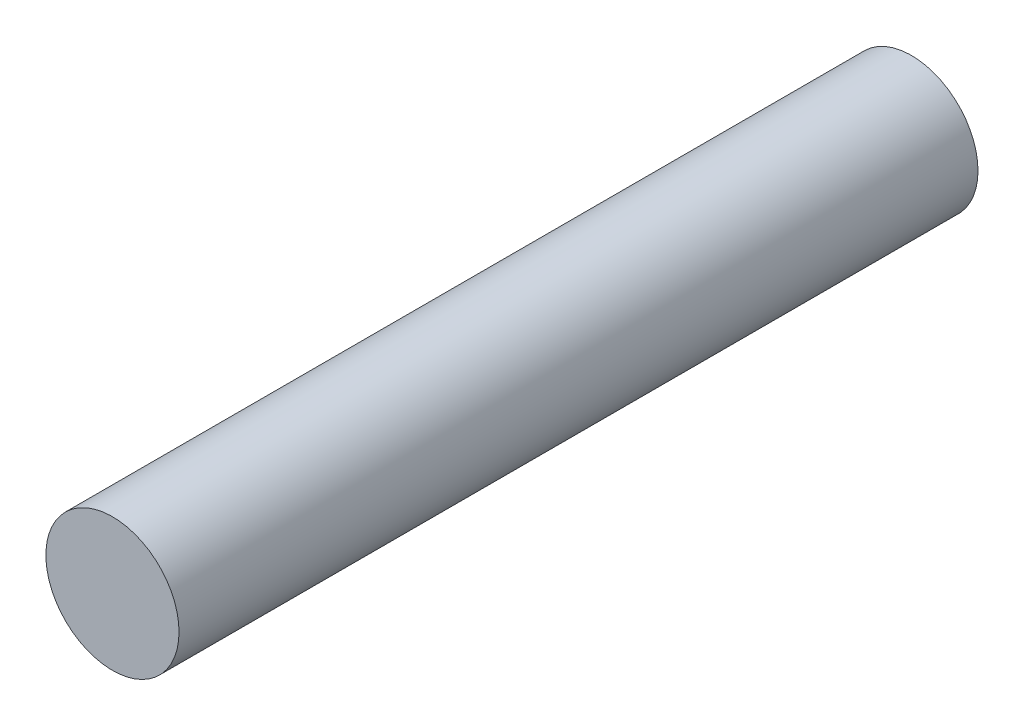
SolidWorks part; units mm, degrees
material "Plain Carbon Steel"
ref_plane "Front Plane" through (0, 0, 0) normal (0, 0, 1) x (1, 0, 0)
ref_plane "Top Plane" through (0, 0, 0) normal (0, 1, 0) x (1, 0, 0)
ref_plane "Right Plane" through (0, 0, 0) normal (1, 0, 0) x (0, 0, -1)
sketch "Sketch1" plane through (0, 0, 0) normal (0, 0, 1) x (1, 0, 0)
  circle A0 centre (0, 0) radius 4.7625
  dimension "D1" = 9.525
extrude "Boss-Extrude1" add sketch "Sketch1" along normal blind 57.15
